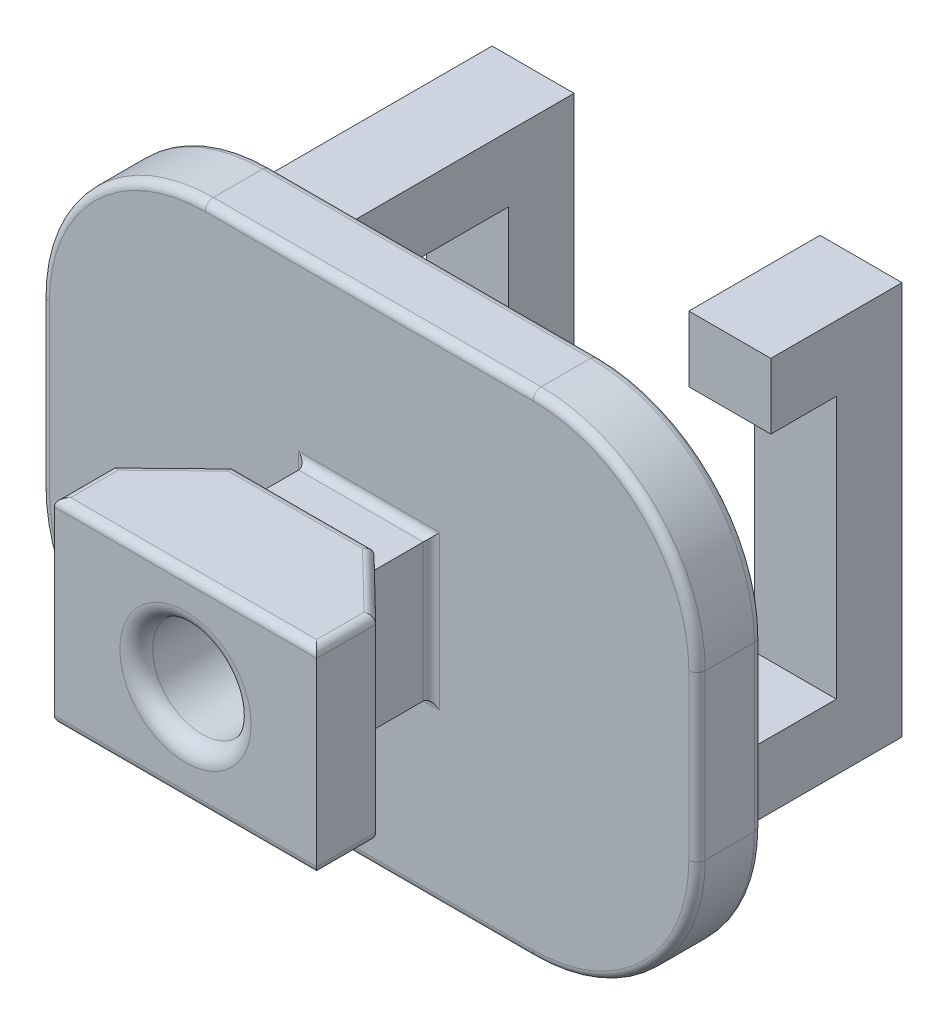
SolidWorks part; units mm, degrees
ref_plane "Front Plane" through (0, 0, 0) normal (0, 0, 1) x (1, 0, 0)
ref_plane "Top Plane" through (0, 0, 0) normal (0, 1, 0) x (1, 0, 0)
ref_plane "Right Plane" through (0, 0, 0) normal (1, 0, 0) x (0, 0, -1)
sketch "Sketch1" plane through (0, 0, 0) normal (0, 1, 0) x (1, 0, 0)
  line L0 (-8, 0) -> (8, 0)
  line L1 (8, 0) -> (8, 3.6)
  line L2 (8, 3.6) -> (4.3, 7.2)
  line L3 (4.3, 7.2) -> (-4.3, 7.2)
  line L4 (-4.3, 7.2) -> (-8, 3.6)
  line L5 (-8, 3.6) -> (-8, 0)
  point P4 (0, 0)
  dimension "D1" = 16
  dimension "D2" = 8.6
  dimension "D3" = 7.2
  dimension "D4" = 3.6
extrude "Boss-Extrude1" add sketch "Sketch1" along normal mid plane 12
sketch "Sketch2" plane through (0, 0, -7.2) normal (0, 0, -1) x (-1, 0, 0)
  line L1 (-3.8, -4.2) -> (3.8, -4.2)
  line L2 (-3.8, -4.2) -> (-3.8, 4.2)
  line L3 (-3.8, 4.2) -> (3.8, 4.2)
  line L4 (3.8, -4.2) -> (3.8, 4.2)
  line L5 (-3.8, -4.2) -> (3.8, 4.2) construction
  line L6 (-3.8, 4.2) -> (3.8, -4.2) construction
  point P0 (0, 0)
  dimension "D1" = 7.6
  dimension "D2" = 8.4
extrude "Boss-Extrude2" add sketch "Sketch2" along normal blind 4
sketch "Sketch3" plane through (0, 0, -11.2) normal (0, 0, -1) x (-1, 0, 0)
  line L1 (-20, -15) -> (20, -15)
  line L2 (-20, -15) -> (-20, 15)
  line L3 (-20, 15) -> (20, 15)
  line L4 (20, -15) -> (20, 15)
  line L5 (-20, -15) -> (20, 15) construction
  line L6 (-20, 15) -> (20, -15) construction
  point P0 (0, 0)
  dimension "D1" = 30
  dimension "D2" = 40
extrude "Boss-Extrude3" add sketch "Sketch3" along normal blind 4
ref_plane "Plane1" through (-10, 0, 0) normal (-1, 0, 0) x (0, 0, 1)
sketch "Sketch6" plane through (-10, 0, 0) normal (-1, 0, 0) x (0, 0, 1)
  line L0 (-15.2, 12) -> (-31.2, 12)
  line L1 (-31.2, 12) -> (-31.2, -12)
  line L2 (-31.2, -12) -> (-23.2, -12)
  line L3 (-23.2, -12) -> (-23.2, -8)
  line L4 (-23.2, -8) -> (-27.2, -8)
  line L5 (-27.2, -8) -> (-27.2, 8)
  line L6 (-27.2, 8) -> (-15.2, 8)
  line L7 (-15.2, 8) -> (-15.2, 12)
  line L8 (-15.2, -15) -> (-15.2, 15) construction
  line L9 (-15.2, -15) -> (-15.2, 15)
  line L10 (-15.2, 15) -> (-11.2, 15) construction
  line L11 (-15.2, -15) -> (-11.2, -15) construction
  point P10 (0, 0)
  dimension "D1" = 4
  dimension "D2" = 4
  dimension "D3" = 4
  dimension "D4" = 8
  dimension "D5" = 4
  dimension "D6" = 3
  dimension "D7" = 3
extrude "Boss-Extrude4" add sketch "Sketch6" along normal mid plane 5 contours L6 L7 L0 L1 L2 L3 L4 L5
ref_plane "Plane2" through (10, 0, 0) normal (1, 0, 0) x (0, 0, -1)
sketch "Sketch7" plane through (10, 0, 0) normal (1, 0, 0) x (0, 0, -1)
  line L0 (23.2, 8) -> (23.2, 12)
  line L1 (15.2, 15) -> (15.2, -15) construction
  line L2 (15.2, 15) -> (15.2, -15)
  line L3 (15.2, -12) -> (15.2, -8)
  line L4 (15.2, -8) -> (27.2, -8)
  line L5 (27.2, 8) -> (23.2, 8)
  line L6 (23.2, 12) -> (31.2, 12)
  line L7 (31.2, -12) -> (15.2, -12)
  line L8 (15.2, 8) -> (27.2, 8)
  line L9 (27.2, 8) -> (27.2, -8)
  line L10 (27.2, -8) -> (23.2, -8)
  line L11 (23.2, -8) -> (23.2, -12)
  line L12 (23.2, -12) -> (31.2, -12)
  line L13 (31.2, -12) -> (31.2, 12)
  line L14 (31.2, 12) -> (15.2, 12)
  line L15 (15.2, 12) -> (15.2, 8)
  line L16 (23.2, 8) -> (27.2, 8)
  line L17 (27.2, 8) -> (27.2, -8)
  line L18 (27.2, -8) -> (15.2, -8)
  line L20 (15.2, -12) -> (31.2, -12)
  line L21 (31.2, -12) -> (31.2, 12)
  line L22 (31.2, 12) -> (23.2, 12)
  line L23 (15.2, 12) -> (15.2, 8)
  dimension "D2" = 4
  dimension "D1" = 0
extrude "Boss-Extrude5" add sketch "Sketch7" along normal mid plane 5 contours L7 L21 L6 L0 L5 L17 L4 L2
fillet "Fillet1" radius 10 4 edges at (-20, -15, -13.2) (-20, 15, -13.2) (20, -15, -13.2) (20, 15, -13.2)
sketch "Sketch8" plane through (0, 0, 0) normal (0, 0, 1) x (1, 0, 0)
  circle A0 centre (0, 0) radius 3
  dimension "D1" = 6
extrude "Cut-Extrude1" cut sketch "Sketch8" against normal through all
fillet "Fillet2" radius 1 2 edges at (3, 0, 0) (3, 0, -15.2)
fillet "Fillet3" radius 0.5 12 edges at (8, 6, -1.8) (0, 6, 0) (-8, 6, -1.8) (-6.15, 6, -5.4) (0, 6, -7.2) (6.15, 6, -5.4) (0, -6, -7.2) (-6.15, -6, -5.4) (-8, -6, -1.8) (0, -6, 0) (8, -6, -1.8) (6.15, -6, -5.4)
fillet "Fillet4" radius 0.5 16 edges at (20, 0, -11.2) (17.0711, -12.0711, -11.2) (0, -15, -11.2) (-17.0711, -12.0711, -11.2) (-20, 0, -11.2) (-17.0711, 12.0711, -11.2) (0, 15, -11.2) (0, 15, -15.2) (-17.0711, 12.0711, -15.2) (-20, 0, -15.2) (-17.0711, -12.0711, -15.2) (0, -15, -15.2) (17.0711, -12.0711, -15.2) (20, 0, -15.2) (17.0711, 12.0711, -11.2) (17.0711, 12.0711, -15.2)
fillet "Fillet5" radius 0.5 4 edges at (0, -4.2, -11.2) (3.8, 0, -11.2) (0, 4.2, -11.2) (-3.8, 0, -11.2)
